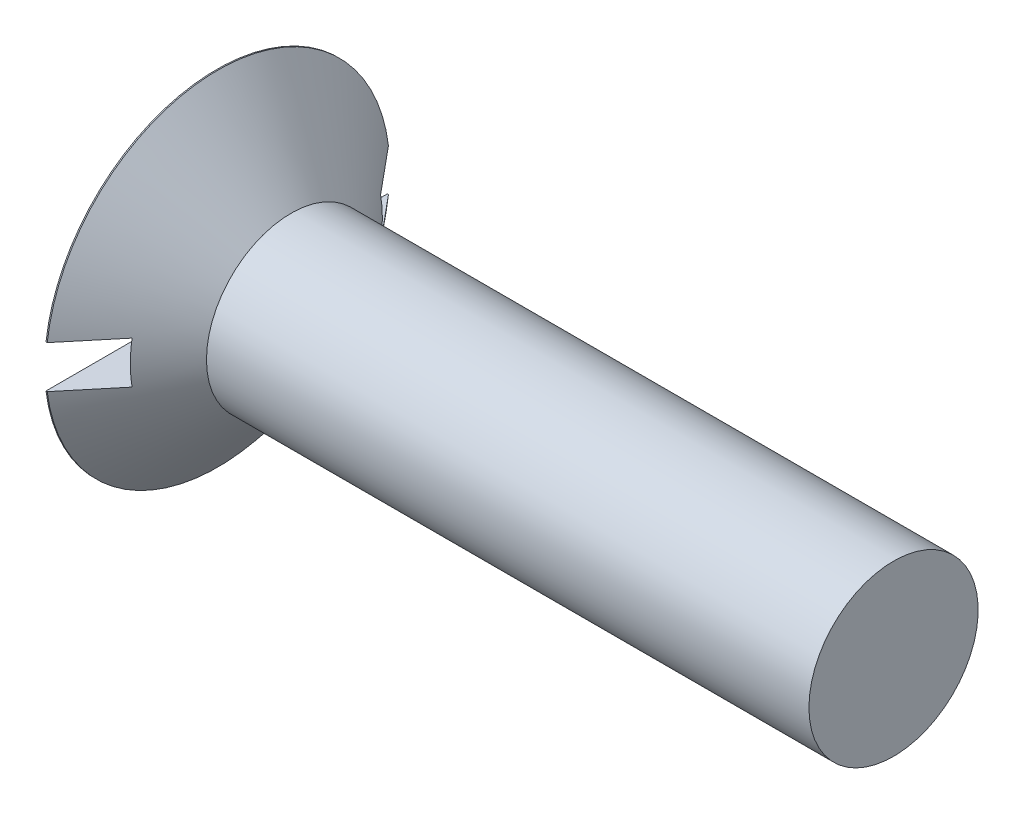
SolidWorks part; units mm, degrees
ref_plane "Plane1" through (0, 0, 0) normal (0, 0, 1) x (1, 0, 0)
ref_plane "Plane2" through (0, 0, 0) normal (0, 1, 0) x (1, 0, 0)
ref_plane "Plane3" through (0, 0, 0) normal (1, 0, 0) x (0, 0, -1)
sketch "BodySke" plane through (0, 0, 0) normal (0, 0, 1) x (1, 0, 0)
  line L0 (0, 0) -> (0, 9.6774)
  line L1 (0, 9.6774) -> (0.0669, 9.6774)
  line L2 (4.191, 4.7625) -> (38.1, 4.7625)
  line L3 (38.1, 4.7625) -> (38.1, 0)
  line L4 (38.1, 0) -> (0, 0)
  line L5 (-6.35, 0) -> (82.55, 0) construction
  line L6 (4.191, -4.7625) -> (38.1, -4.7625) construction
  line L7 (0.0669, -9.6774) -> (4.191, -4.7625) construction
  line L8 (0.0669, 9.6774) -> (4.191, 4.7625)
  line L9 (0, -9.6774) -> (0.0669, -9.6774) construction
  line L10 (5.7785, 6.35) -> (5.7785, -3.175) construction
  line L11 (6.35, 6.35) -> (6.35, -3.175) construction
  dimension "Diameter" = 9.525
  dimension "Length" = 38.1
  dimension "Head_ht" = 4.191
  dimension "Head_dia" = 19.3548
  dimension "Head_ang" = 100
  dimension "D6" = 0.0669
  dimension "Advance" = 1.5875
  dimension "Thread_nom" = 31.75
revolve "Base-Revolve" add sketch "BodySke" angle 360 about L5
cosmetic thread "ThreadCosmetic" [suppressed] parameters "Thread_length"=31.75, "Thread_minor"=7.9248
sketch "Sketch2" plane through (0, 0, 0) normal (-1, 0, 0) x (0, 0, 1)
  line L0 (-9.6774, -1.1938) -> (9.6774, -1.1938)
  line L1 (-9.6774, -1.1938) -> (-9.6774, 1.1938)
  line L2 (9.6774, 1.1938) -> (-9.6774, 1.1938)
  line L3 (9.6774, 1.1938) -> (9.6774, -1.1938)
  dimension "D1" = 1.1938
  dimension "Slot_width" = 2.3876
  dimension "D2" = 19.3548
  dimension "D3" = 9.6774
extrude "Slot" cut sketch "Sketch2" against normal blind 2.2352
sketch "Sketch3" plane through (0, 0, 0) normal (-1, 0, 0) x (0, 0, 1)
  line L0 (-1.0922, 6.6421) -> (1.0922, 6.6421)
  line L1 (1.0922, 6.6421) -> (1.0922, -6.6421)
  line L2 (1.0922, -6.6421) -> (-1.0922, -6.6421)
  line L3 (-1.0922, -6.6421) -> (-1.0922, 6.6421)
  dimension "D1" = 6.6421
  dimension "Cross_dia" = 13.2842
  dimension "D2" = 1.0922
  dimension "Cross_width" = 2.1844
ref_plane "Plane4" through (7.9756, 0, 0) normal (-1, 0, 0) x (0, 0, 1)
sketch "Sketch4" plane through (7.9756, 0, 0) normal (-1, 0, 0) x (0, 0, 1)
  line L0 (-0.5461, 0.5461) -> (0.5461, 0.5461)
  line L3 (0.5461, 0.5461) -> (0.5461, -0.5461)
  line L4 (0.5461, -0.5461) -> (-0.5461, -0.5461)
  line L5 (-0.5461, -0.5461) -> (-0.5461, 0.5461)
  dimension "D1" = 1.0922
  dimension "D2" = 1.0922
  dimension "D3" = 0.5461
  dimension "D4" = 0.5461
loft "Cross" cut profiles "Sketch3", "Sketch4"
pattern_circular "CirPattern1" count 2 every 90 about axis through (0, 0, 0) along (1, 0, 0) of "Cross"
sketch "ThdSchSke" plane through (0, 0, 0) normal (0, 0, 1) x (1, 0, 0)
  line L0 (6.35, -3.9624) -> (5.7898, -4.7625)
  line L1 (6.35, -3.9624) -> (6.9103, -4.7625)
  line L2 (6.9103, -4.7625) -> (6.9103, -5.9531)
  line L3 (-3.175, 0) -> (5.1513, 0) construction
  line L5 (6.9103, -5.9531) -> (5.7898, -5.9531)
  line L6 (5.7898, -5.9531) -> (5.7898, -4.7625)
  line L7 (0, 9.6774) -> (0, 1.1938) construction
  dimension "Thread_minor" = 7.9248
  dimension "Diameter" = 9.525
  dimension "Start" = 6.35
  dimension "SideAngle" = 55
  dimension "VeeAngle" = 70
  dimension "Overcut" = 11.9063
revolve "ThreadSchematic" [suppressed] cut sketch "ThdSchSke" angle 360 about L3
pattern_linear "ThdSchPat" [suppressed]
equation "\"D1@Sketch3\" = \"Cross_dia@Sketch3\" / 2"
equation "\"D2@Sketch3\" = \"Cross_width@Sketch3\" / 2"
equation "\"D1@Sketch4\" = \"Cross_width@Sketch3\" *.5"
equation "\"D2@Sketch4\" = \"D1@Sketch4\""
equation "\"D4@Sketch4\" = \"D2@Sketch4\" / 2"
equation "\"D3@Sketch4\" = \"D1@Sketch4\" / 2"
equation "\"D1@Sketch2\" = \"Slot_width@Sketch2\" / 2"
equation "\"D2@Sketch2\" = \"Head_dia@BodySke\""
equation "\"D3@Sketch2\" = \"D2@Sketch2\" / 2"
equation "\"Thread_length@ThreadCosmetic\" = ((sgn( (\"Length@BodySke\" - \"Advance@BodySke\" - \"Head_ht@BodySke\" ) - \"Thread_nom@BodySke\" )-1)*( (\"Length@BodySke\" - \"Advance@BodySke\" - \"Head_ht@BodySke\" ) - \"Thread_nom@BodySke\" ))/-2+ \"Thread_nom@BodySke\""
equation "\"Thread_minor@ThdSchSke\" = \"Thread_minor@ThreadCosmetic\""
equation "\"Diameter@ThdSchSke\" = \"Diameter@BodySke\""
equation "\"Overcut@ThdSchSke\" = \"Diameter@BodySke\" * 1.25"
equation "\"Start@ThdSchSke\" = 0.000001 + \"Length@BodySke\" - \"Thread_length@ThreadCosmetic\"  '---Countersunk---"
equation "\"Num_threads@ThdSchPat\" = int( \"Thread_length@ThreadCosmetic\" / \"Advance@BodySke\" + 0.999 )  + 1"
equation "\"Advance@ThdSchPat\" = \"Thread_length@ThreadCosmetic\" /  (\"Num_threads@ThdSchPat\" - 1) 'relax it"
